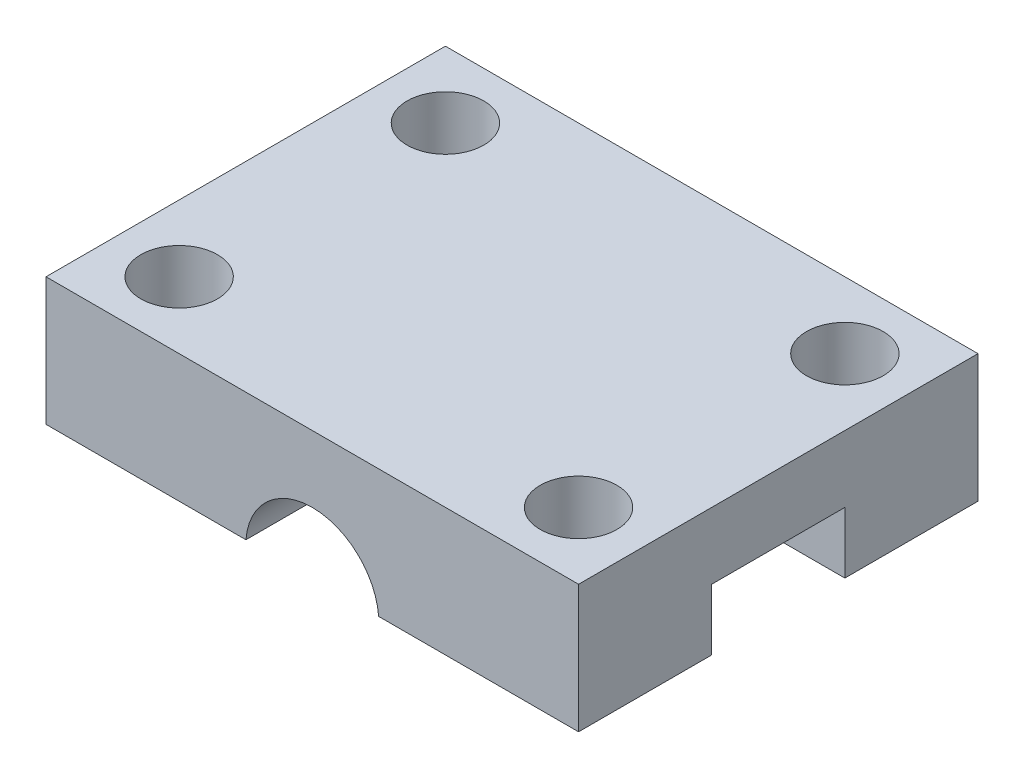
SolidWorks part; units mm, degrees
ref_plane "Front Plane" through (0, 0, 0) normal (0, 0, 1) x (1, 0, 0)
ref_plane "Top Plane" through (0, 0, 0) normal (0, 1, 0) x (1, 0, 0)
ref_plane "Right Plane" through (0, 0, 0) normal (1, 0, 0) x (0, 0, -1)
sketch "Sketch1" plane through (0, 0, 0) normal (1, 0, 0) x (0, 0, -1)
  line L0 (9.525, -0.254) -> (9.525, 0) construction
  line L1 (0, 0) -> (19.05, 0)
  line L2 (0, 0) -> (0, 6.096)
  line L3 (0, 6.096) -> (19.05, 6.096)
  line L4 (19.05, 0) -> (19.05, 6.096)
  line L5 (9.525, 2.921) -> (9.525, 6.096) construction
  line L7 (12.7, 2.921) -> (6.35, 2.921)
  line L8 (6.35, 2.921) -> (6.35, -3.429)
  line L9 (6.35, -3.429) -> (12.7, -3.429)
  line L10 (12.7, -3.429) -> (12.7, 2.921)
  circle A1 centre (9.525, -0.254) radius 3.175 construction
  dimension "D1" = 6.35
  dimension "D2" = 0.254
  dimension "D3" = 19.05
  dimension "D4" = 3.175
extrude "Boss-Extrude1" add sketch "Sketch1" along normal blind 25.4
sketch "Sketch2" plane through (0, 0, 0) normal (0, 0, 1) x (1, 0, 0)
  line L0 (25.4, 0) -> (0, 0) construction
  line L1 (12.7, -0.254) -> (12.7, 0) construction
  circle A0 centre (12.7, -0.254) radius 3.175
  dimension "D2" = 6.35
  dimension "D1" = 0.254
extrude "Cut-Extrude2" cut sketch "Sketch2" against normal through all
sketch "Sketch4" plane through (0, 0, 0) normal (0, -1, 0) x (1, 0, 0)
  line L0 (3.175, -3.175) -> (3.175, 0) construction
  line L1 (3.175, -3.175) -> (3.175, -6.35) construction
  line L2 (3.175, -15.875) -> (3.175, -12.7) construction
  line L3 (3.175, -15.875) -> (3.175, -19.05) construction
  line L4 (22.225, -3.175) -> (22.225, 0) construction
  line L5 (22.225, -3.175) -> (22.225, -6.35) construction
  line L6 (22.225, -15.875) -> (22.225, -12.7) construction
  line L7 (22.225, -15.875) -> (22.225, -19.05) construction
  line L10 (25.4, 0) -> (15.8648, 0) construction
  line L11 (9.5352, -19.05) -> (0, -19.05) construction
  line L12 (12.7, -12.7) -> (0, -12.7) construction
  line L13 (12.7, -6.35) -> (0, -6.35) construction
  line L14 (9.5352, 0) -> (0, 0) construction
  line L15 (25.4, 0) -> (25.4, -6.35) construction
  line L16 (0, -12.7) -> (0, -6.35) construction
  line L17 (25.4, -6.35) -> (15.8648, -6.35) construction
  line L18 (25.4, -19.05) -> (15.8648, -19.05) construction
  line L19 (25.4, -12.7) -> (12.7, -12.7) construction
  circle A0 centre (3.175, -3.175) radius 1.8288
  circle A1 centre (3.175, -15.875) radius 1.8288
  circle A2 centre (22.225, -3.175) radius 1.8288
  circle A3 centre (22.225, -15.875) radius 1.8288
  dimension "D1" = 3.6576
  dimension "D2" = 3.6576
  dimension "D3" = 3.6576
  dimension "D4" = 3.6576
  dimension "D5" = 3.175
  dimension "D6" = 3.175
extrude "Cut-Extrude3" cut sketch "Sketch4" against normal through all
